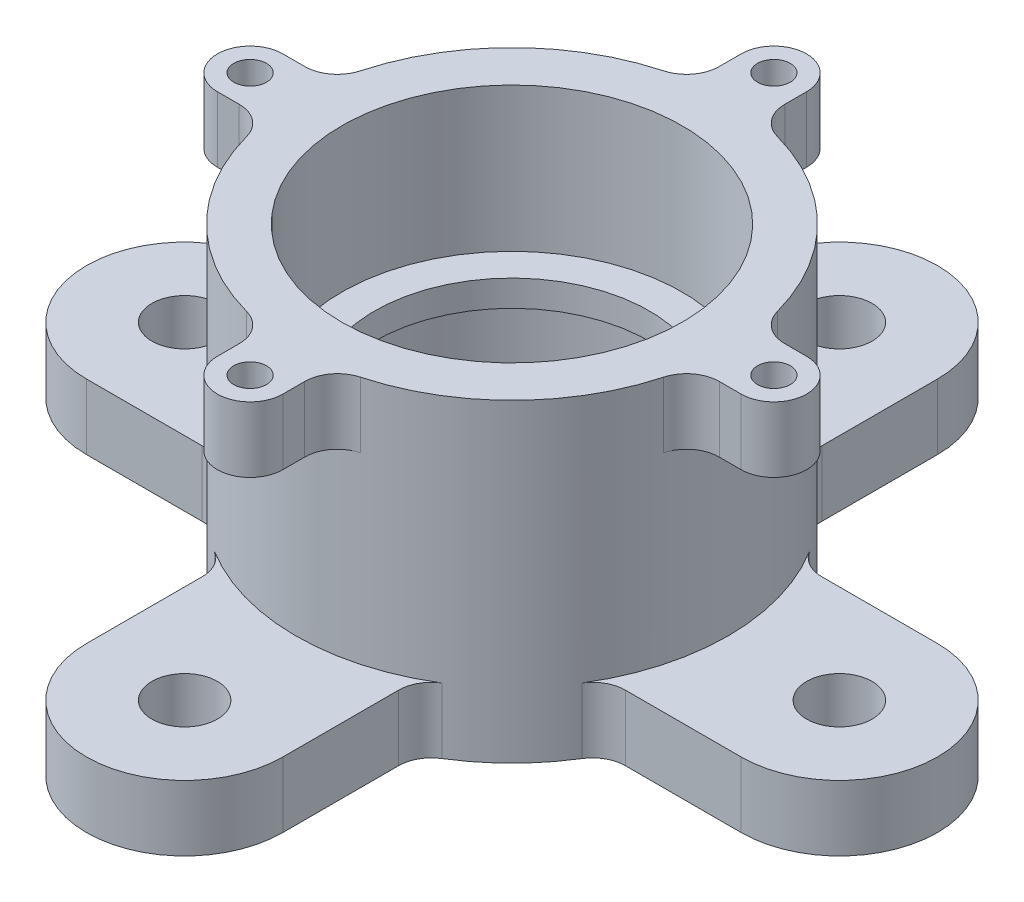
SolidWorks part; units mm, degrees
material "Plain Carbon Steel"
ref_plane "Front Plane" through (0, 0, 0) normal (0, 0, 1) x (1, 0, 0)
ref_plane "Top Plane" through (0, 0, 0) normal (0, 1, 0) x (1, 0, 0)
ref_plane "Right Plane" through (0, 0, 0) normal (1, 0, 0) x (0, 0, -1)
sketch "Sketch1" plane through (0, 0, 0) normal (0, 0, 1) x (1, 0, 0)
  line L0 (0, 27.1824) -> (0, -27.1824) construction
  line L1 (26, 24) -> (26, 2)
  line L2 (26, 2) -> (21, 2)
  line L3 (21, 2) -> (21, -2)
  line L4 (21, -2) -> (26, -2)
  line L5 (26, -2) -> (26, -24)
  line L6 (26, -24) -> (33, -24)
  line L7 (33, -24) -> (33, 24)
  line L8 (33, 24) -> (26, 24)
  line L9 (-36.1848, 0) -> (36.1848, 0) construction
  point P4 (0, 0)
  point P17 (0, 0)
  dimension "D1" = 52
  dimension "D2" = 7
  dimension "D3" = 4
  dimension "D4" = 48
  dimension "D5" = 42
revolve "Revolve1" add sketch "Sketch1" angle 360 about L0
sketch "Sketch2" plane through (0, 24, 0) normal (0, -1, 0) x (1, 0, 0)
  line L0 (0, 0) -> (0, 44.2475) construction
  line L1 (5, 40) -> (5, 32.619)
  line L13 (-5, 40) -> (-5, 32.619)
  line L23 (40, -5) -> (32.619, -5)
  line L24 (40, 5) -> (32.619, 5)
  line L25 (-5, -40) -> (-5, -32.619)
  line L26 (5, -40) -> (5, -32.619)
  line L27 (-40, 5) -> (-32.619, 5)
  line L28 (-40, -5) -> (-32.619, -5)
  circle A13 centre (0, 0) radius 33 construction
  arc A14 (5, 32.619) -> (-5, 32.619) centre (0, 0) ccw
  circle A15 centre (0, 40) radius 2.5
  arc A22 (5, 40) -> (-5, 40) centre (0, 40) ccw
  arc A23 (32.619, -5) -> (32.619, 5) centre (0, 0) ccw
  circle A24 centre (40, 0) radius 2.5
  arc A25 (40, -5) -> (40, 5) centre (40, 0) ccw
  arc A26 (-5, -32.619) -> (5, -32.619) centre (0, 0) ccw
  circle A27 centre (0, -40) radius 2.5
  arc A28 (-5, -40) -> (5, -40) centre (0, -40) ccw
  arc A29 (-32.619, 5) -> (-32.619, -5) centre (0, 0) ccw
  circle A30 centre (-40, 0) radius 2.5
  arc A31 (-40, 5) -> (-40, -5) centre (-40, 0) ccw
  point P31 (0, 0)
  dimension "D1" = 5
  dimension "D3" = 40
  dimension "D4" = 5
extrude "Boss-Extrude1" add sketch "Sketch2" along normal blind 10
sketch "Sketch3" plane through (0, -24, 0) normal (0, 1, 0) x (-1, 0, 0)
  line L0 (-15, 50) -> (-15, 29.3939)
  line L1 (15, 50) -> (15, 29.3939)
  line L2 (0, 58.6215) -> (0, -58.6215) construction
  line L3 (50, 15) -> (29.3939, 15)
  line L4 (50, -15) -> (29.3939, -15)
  line L5 (15, -50) -> (15, -29.3939)
  line L6 (-15, -50) -> (-15, -29.3939)
  line L7 (-50, -15) -> (-29.3939, -15)
  line L8 (-50, 15) -> (-29.3939, 15)
  arc A1 (-15, 50) -> (15, 50) centre (0, 50) cw
  arc A2 (-15, 29.3939) -> (15, 29.3939) centre (0, 0) cw
  circle A3 centre (0, 0) radius 33 construction
  circle A4 centre (0, 50) radius 5
  arc A5 (50, 15) -> (50, -15) centre (50, 0) cw
  arc A6 (29.3939, 15) -> (29.3939, -15) centre (0, 0) cw
  circle A7 centre (50, 0) radius 5
  arc A8 (15, -50) -> (-15, -50) centre (0, -50) cw
  arc A9 (15, -29.3939) -> (-15, -29.3939) centre (0, 0) cw
  circle A10 centre (0, -50) radius 5
  arc A11 (-50, -15) -> (-50, 15) centre (-50, 0) cw
  arc A12 (-29.3939, -15) -> (-29.3939, 15) centre (0, 0) cw
  circle A13 centre (-50, 0) radius 5
  point P13 (0, 0)
  point P33 (0, 0)
  dimension "D1" = 15
  dimension "D3" = 10
  dimension "D2" = 50
  dimension "D4" = 4
extrude "Boss-Extrude2" add sketch "Sketch3" along normal blind 10
fillet "Fillet1" radius 5 16 edges at (-15, -19, 29.3939) (-29.3939, -19, 15) (-29.3939, -19, -15) (-15, -19, -29.3939) (15, -19, -29.3939) (29.3939, -19, -15) (29.3939, -19, 15) (15, -19, 29.3939) (-5, 19, 32.619) (5, 19, 32.619) (-32.619, 19, 5) (-32.619, 19, -5) (-5, 19, -32.619) (5, 19, -32.619) (32.619, 19, -5) (32.619, 19, 5)
